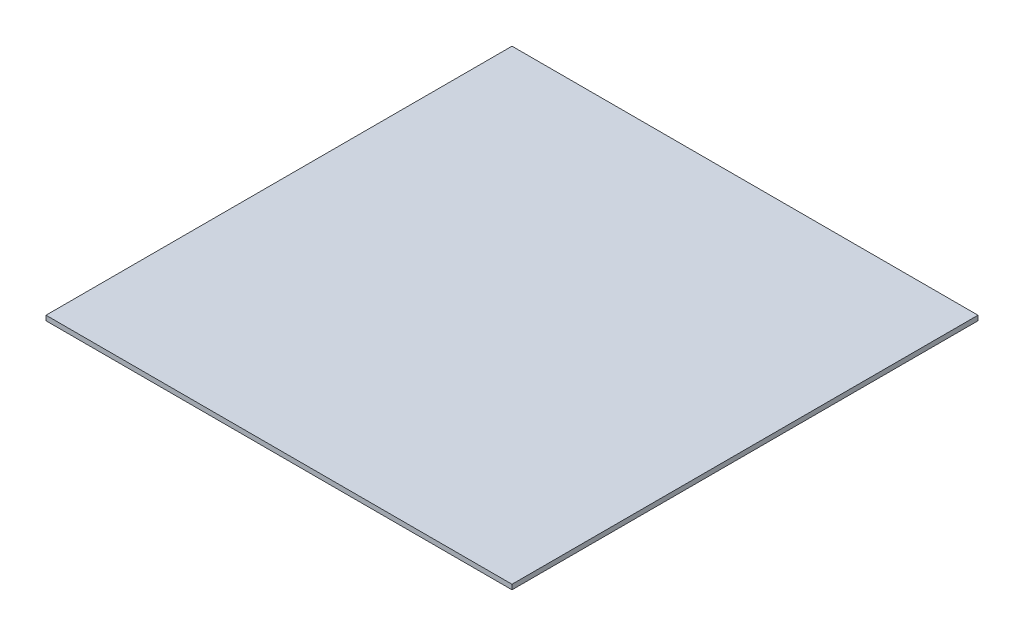
SolidWorks part; units mm, degrees
material "Beech"
ref_plane "Front Plane" through (0, 0, 0) normal (0, 0, 1) x (1, 0, 0)
ref_plane "Top Plane" through (0, 0, 0) normal (0, 1, 0) x (1, 0, 0)
ref_plane "Right Plane" through (0, 0, 0) normal (1, 0, 0) x (0, 0, -1)
sketch "Sketch1" plane through (0, 0, 0) normal (0, 1, 0) x (1, 0, 0)
  line L1 (0, 0) -> (1219.2, 0)
  line L2 (0, 0) -> (0, -1219.2)
  line L3 (0, -1219.2) -> (1219.2, -1219.2)
  line L4 (1219.2, 0) -> (1219.2, -1219.2)
  point P5 (238.8957, -428.8499)
  point P6 (545.9993, -1755.4503)
  point P7 (591.2349, -2077.546)
  point P8 (756.7918, 0)
  point P9 (1928.5497, 0)
  point P10 (1239.7624, 0)
  point P11 (1220.3494, 0)
extrude "Boss-Extrude1" add sketch "Sketch1" along normal blind 12.7 contours L2 L3 L4 L1
